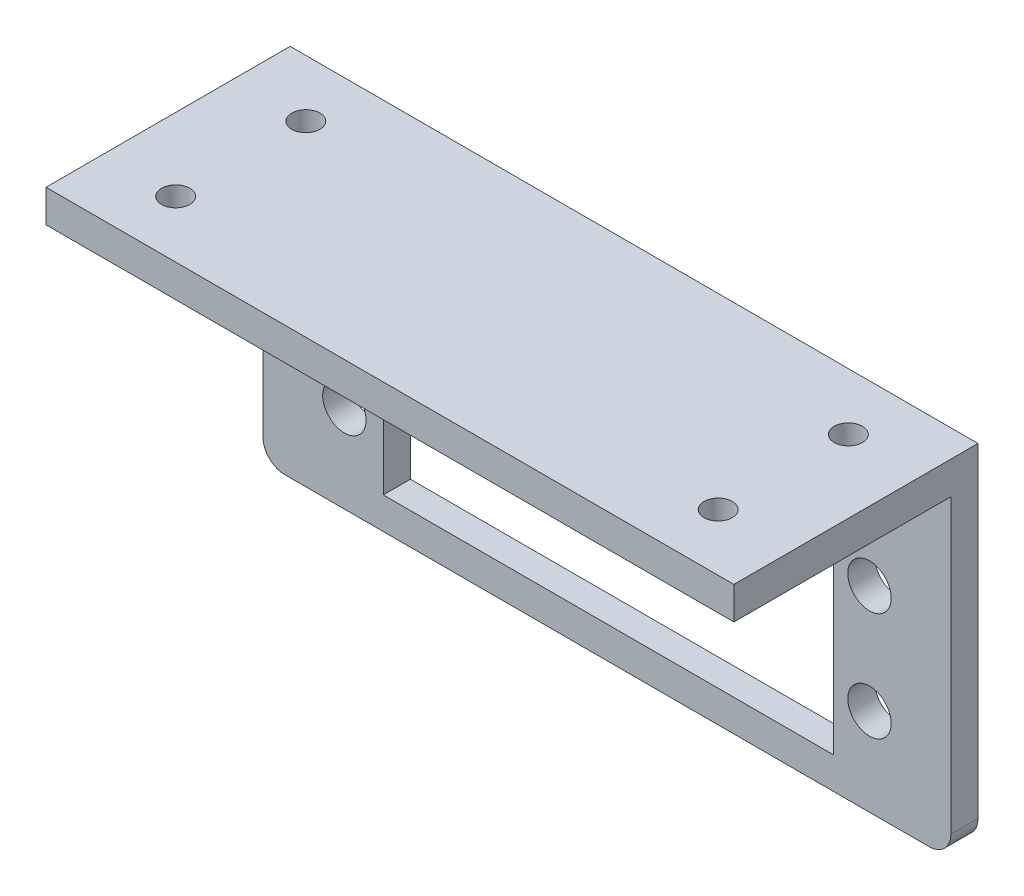
SolidWorks part; units mm, degrees
ref_plane "前视基准面" through (0, 0, 0) normal (0, 0, 1) x (1, 0, 0)
ref_plane "上视基准面" through (0, 0, 0) normal (0, 1, 0) x (1, 0, 0)
ref_plane "右视基准面" through (0, 0, 0) normal (1, 0, 0) x (0, 0, -1)
sketch "草图1" plane through (0, 0, 0) normal (0, 0, 1) x (1, 0, 0)
  line L0 (9.1028, -4.3603) -> (68.5028, -4.3603)
  line L5 (7.1028, -2.3603) -> (7.1028, 27.5775)
  line L6 (7.1028, 27.5775) -> (70.5028, 27.5775)
  line L7 (70.5028, -2.3603) -> (70.5028, 27.5775)
  line L8 (14.6028, 13.7152) -> (18.5128, 13.7152) construction
  line L9 (18.5128, 13.7152) -> (18.5128, -0.4972) construction
  line L10 (14.6028, 3.7152) -> (14.6028, -1.1848) construction
  line L11 (14.6028, -1.1848) -> (22.2744, -1.1848) construction
  line L12 (18.5128, -0.4972) -> (18.5128, -3.6091) construction
  line L13 (18.1886, -1.4348) -> (18.1886, 19.0652)
  line L18 (18.1886, 19.0652) -> (59.6886, 19.0652)
  line L19 (59.6886, -1.4348) -> (59.6886, 19.0652)
  line L20 (18.1886, -1.4348) -> (59.6886, -1.4348)
  circle A0 centre (14.6028, 13.7152) radius 2
  circle A1 centre (14.6028, 3.7152) radius 2
  circle A2 centre (63.0028, 3.7152) radius 2
  circle A3 centre (63.0028, 13.7152) radius 2
  arc A4 (70.5028, -2.3603) -> (68.5028, -4.3603) centre (68.5028, -2.3603) cw
  arc A5 (7.1028, -2.3603) -> (9.1028, -4.3603) centre (9.1028, -2.3603) ccw
  dimension "D1" = 2
  dimension "D2" = 3.91
  dimension "D3" = 4.9
extrude "凸台-拉伸1" add sketch "草图1" along normal blind 2.5
sketch "草图2" plane through (0, 0, 2.5) normal (0, 0, 1) x (1, 0, 0)
  line L0 (70.5028, -2.3603) -> (70.5028, 27.5775) construction
  line L1 (7.1028, 27.5775) -> (70.5028, 27.5775)
  line L2 (7.1028, 27.5775) -> (7.1028, 24.5775)
  line L3 (7.1028, 24.5775) -> (70.5028, 24.5775)
  line L4 (70.5028, 27.5775) -> (70.5028, 24.5775)
  dimension "D1" = 3
extrude "凸台-拉伸2" add sketch "草图2" along normal blind 20
sketch "草图3" plane through (0, 27.5775, 0) normal (0, 1, 0) x (1, 0, 0)
  line L0 (38.8028, 0) -> (38.8028, -28.7779) construction
  line L1 (70.5028, 0) -> (7.1028, 0) construction
  line L2 (70.5028, -11.25) -> (7.1028, -11.25) construction
  line L3 (70.5028, -22.5) -> (70.5028, 0) construction
  line L4 (7.1028, -22.5) -> (7.1028, 0) construction
  circle A0 centre (13.8028, -5.25) radius 1.3
  circle A1 centre (63.8028, -5.25) radius 1.3
  circle A2 centre (63.8028, -17.25) radius 1.3
  circle A3 centre (13.8028, -17.25) radius 1.3
  dimension "D1" = 2.6
  dimension "D2" = 50
  dimension "D3" = 12
extrude "切除-拉伸1" cut sketch "草图3" against normal up to surface (3 mm away) up to face at (38.8028, 24.5775, 12.5)
